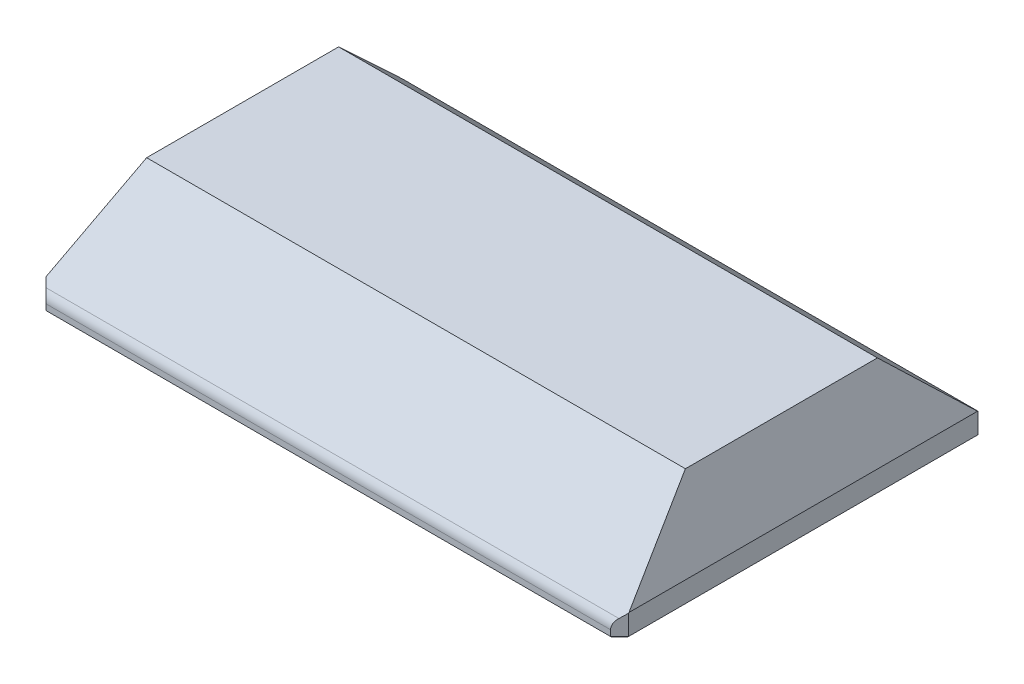
SolidWorks part; units mm, degrees
ref_plane "Front Plane" through (0, 0, 0) normal (0, 0, 1) x (1, 0, 0)
ref_plane "Top Plane" through (0, 0, 0) normal (0, 1, 0) x (1, 0, 0)
ref_plane "Right Plane" through (0, 0, 0) normal (1, 0, 0) x (0, 0, -1)
sketch "Sketch1" plane through (0, 0, 0) normal (0, 1, 0) x (1, 0, 0)
  line L1 (-65, -41) -> (65, -41)
  line L2 (-65, -41) -> (-65, 41)
  line L3 (-65, 41) -> (65, 41)
  line L4 (65, -41) -> (65, 41)
  line L5 (-65, -41) -> (65, 41) construction
  line L6 (-65, 41) -> (65, -41) construction
  point P0 (0, 0)
  dimension "D1" = 130
  dimension "D2" = 82
ref_plane "Plane1" through (0, 22, 0) normal (0, 1, 0) x (1, 0, 0)
sketch "Sketch2" plane through (0, 22, 0) normal (0, 1, 0) x (1, 0, 0)
  line L1 (-60, -23) -> (60, -23)
  line L2 (-60, -23) -> (-60, 23)
  line L3 (-60, 23) -> (60, 23)
  line L4 (60, -23) -> (60, 23)
  line L5 (-60, -23) -> (60, 23) construction
  line L6 (-60, 23) -> (60, -23) construction
  point P0 (0, 0)
  dimension "D1" = 46
  dimension "D2" = 120
extrude "Boss-Extrude1" add sketch "Sketch1" along normal blind 5
sketch "Sketch3" plane through (0, 5, 0) normal (0, 1, 0) x (1, 0, 0)
  line L4 (65, -41) -> (65, 41)
  line L5 (65, 41) -> (-65, 41)
  line L6 (-65, 41) -> (-65, -41)
  line L7 (-65, -41) -> (65, -41)
  line L8 (65, -41) -> (65, 41)
  line L9 (65, 41) -> (-65, 41)
  line L10 (-65, 41) -> (-65, -41)
  line L11 (-65, -41) -> (65, -41)
  dimension "D1" = 0
loft "Loft2" add profiles "Sketch3", "Sketch2"
chamfer "Chamfer1" distance 2 angle 45 4 edges at (-65, 2.5, 41) (65, 2.5, 41) (65, 2.5, -41) (-65, 2.5, -41)
sketch "Sketch4" plane through (0, 0, 0) normal (0, -1, 0) x (1, 0, 0)
  line L0 (0, 41) -> (0, -41) construction
  line L1 (-63, 41) -> (63, 41) construction
  line L2 (63, -41) -> (-63, -41) construction
  line L3 (-40, -37.5) -> (40, -37.5) construction
  circle A0 centre (40, -37.5) radius 1.2
  circle A1 centre (-40, -37.5) radius 1.2
  point P9 (0, -37.5)
  dimension "D3" = 2.4
  dimension "D1" = 3.5
  dimension "D2" = 80
extrude "Cut-Extrude1" cut sketch "Sketch4" against normal blind 4
sketch "Sketch5" plane through (0, 0, 0) normal (0, -1, 0) x (1, 0, 0)
  line L1 (-57, -20) -> (57, -20)
  line L2 (-57, -20) -> (-57, 20)
  line L3 (-57, 20) -> (57, 20)
  line L4 (57, -20) -> (57, 20)
  line L5 (-57, -20) -> (57, 20) construction
  line L6 (-57, 20) -> (57, -20) construction
  point P0 (0, 0)
  dimension "D1" = 40
  dimension "D2" = 114
extrude "Cut-Extrude2" cut sketch "Sketch5" against normal offset from surface (21 mm away) 1 up to face at (0, 22, 0)
mirror "Mirror1" about plane through (0, 0, 0) normal (0, 0, 1) of "Cut-Extrude1"
sketch "Sketch6" plane through (0, 0, 0) normal (0, -1, 0) x (1, 0, 0)
  line L0 (-57, 20) -> (-57, -20) construction
  line L1 (-59, -28) -> (59, -28)
  line L2 (-59, -28) -> (-59, 28)
  line L3 (-59, 28) -> (59, 28)
  line L4 (59, -28) -> (59, 28)
  line L5 (-59, -28) -> (59, 28) construction
  line L6 (-59, 28) -> (59, -28) construction
  line L7 (-57, 20) -> (57, 20) construction
  point P0 (0, 0)
  dimension "D1" = 2
  dimension "D2" = 8
extrude "Cut-Extrude3" cut sketch "Sketch6" against normal blind 12
ref_plane "Plane2" through (0, 4, 0) normal (0, -1, 0) x (-1, 0, 0)
sketch "Sketch8" plane through (0, 4, 0) normal (0, -1, 0) x (-1, 0, 0)
  line L0 (0, 28) -> (0, -41) construction
  line L1 (-59, 28) -> (-52, 28)
  line L2 (-59, 28) -> (-59, 21)
  line L3 (-59, 21) -> (-52, 21)
  line L4 (-52, 28) -> (-52, 21)
  line L5 (59, 28) -> (-59, 28) construction
  line L6 (63, -41) -> (-63, -41) construction
  line L7 (59, 0) -> (-59, 0) construction
  line L8 (59, -28) -> (59, 28) construction
  line L9 (-59, 28) -> (-59, -28) construction
  line L10 (-52, -28) -> (-52, -21)
  line L11 (-59, -21) -> (-52, -21)
  line L12 (-59, -28) -> (-59, -21)
  line L13 (-59, -28) -> (-52, -28)
  line L14 (59, -28) -> (52, -28)
  line L15 (59, -28) -> (59, -21)
  line L16 (59, -21) -> (52, -21)
  line L17 (52, -28) -> (52, -21)
  line L18 (52, 28) -> (52, 21)
  line L19 (59, 21) -> (52, 21)
  line L20 (59, 28) -> (59, 21)
  line L21 (59, 28) -> (52, 28)
  dimension "D1" = 7
extrude "Boss-Extrude2" add sketch "Sketch8" against normal up to surface (8 mm away) up to face at (0, 12, 0)
sketch "Sketch9" plane through (0, 4, 0) normal (0, -1, 0) x (1, 0, 0)
  line L0 (0, 28) -> (0, -41) construction
  line L1 (52, 28) -> (-52, 28) construction
  line L2 (63, -41) -> (-63, -41) construction
  line L3 (59, 0) -> (-59, 0) construction
  line L4 (59, -28) -> (59, 28) construction
  line L5 (-59, 28) -> (-59, -28) construction
  line L6 (-59, 28) -> (-52, 21) construction
  circle A0 centre (-55.5, 24.5) radius 2.1
  circle A1 centre (55.5, 24.5) radius 2.1
  circle A2 centre (55.5, -24.5) radius 2.1
  circle A3 centre (-55.5, -24.5) radius 2.1
  dimension "D1" = 4.2
extrude "Cut-Extrude4" cut sketch "Sketch9" against normal up to surface (8 mm away) up to face at (0, 12, 0)
sketch "Sketch10" plane through (0, 12, 0) normal (0, -1, 0) x (1, 0, 0)
  line L0 (-59, 28) -> (-59, -28) construction
  line L1 (-57, 20) -> (-59, 20)
  line L2 (-57, 20) -> (-57, -20)
  line L3 (-57, -20) -> (-59, -20)
  line L4 (-59, 20) -> (-59, -20)
  line L5 (59, -21) -> (59, 21) construction
  line L6 (57, -20) -> (59, -20)
  line L7 (57, -20) -> (57, 20)
  line L8 (57, 20) -> (59, 20)
  line L9 (59, -20) -> (59, 20)
  line L10 (-57, 20) -> (57, 20) construction
  line L11 (-57, -20) -> (57, -20) construction
extrude "Cut-Extrude5" cut sketch "Sketch10" against normal up to surface (9 mm away) up to face at (0, 21, 0)
sketch "Sketch11" plane through (0, 0, 0) normal (1, 0, 0) x (0, 0, -1)
  line L0 (21, 22) -> (41, 3)
  line L1 (-23, 22) -> (23, 22) construction
  line L2 (41, 5) -> (41, 0) construction
  line L3 (41, 3) -> (41, 5)
  line L4 (41, 5) -> (23, 22)
  line L5 (23, 22) -> (21, 22)
  line L6 (20, 21) -> (20, 12) construction
  line L7 (0, 22) -> (0, 0) construction
  line L8 (-23, 22) -> (-21, 22)
  line L9 (-41, 5) -> (-23, 22)
  line L10 (-41, 3) -> (-41, 5)
  line L11 (-21, 22) -> (-41, 3)
  dimension "D1" = 1
  dimension "D2" = 2
extrude "Cut-Extrude6" cut sketch "Sketch11" against normal through all both and the other way through all
sketch "Sketch12" plane through (0, 0, 0) normal (1, 0, 0) x (0, 0, -1)
  line L0 (-21, 22) -> (21, 22) construction
  line L1 (-41, 23.6) -> (41, 23.6)
  line L2 (-41, 23.6) -> (-41, 21.6)
  line L3 (-41, 21.6) -> (41, 21.6)
  line L4 (41, 23.6) -> (41, 21.6)
  point P6 (0, 0)
  point P8 (0, 0)
  dimension "D1" = 0.4
  dimension "D2" = 2
extrude "Cut-Extrude7" cut sketch "Sketch12" against normal through all both and the other way through all
fillet "Fillet1" radius 3 2 edges at (0, 3, 41) (0, 3, -41)
chamfer "Chamfer2" distance 0.4 angle 45 8 edges at (-64, 0, -40) (-65, 0, 0) (-64, 0, 40) (0, 0, 41) (64, 0, 40) (65, 0, 0) (64, 0, -40) (0, 0, -41)
